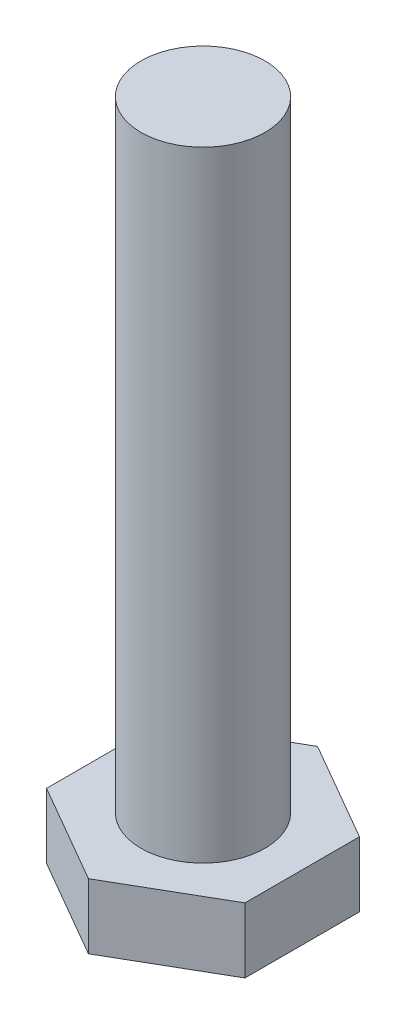
SolidWorks part; units mm, degrees
ref_plane "Спереди" through (0, 0, 0) normal (0, 0, 1) x (1, 0, 0)
ref_plane "Сверху" through (0, 0, 0) normal (0, 1, 0) x (1, 0, 0)
ref_plane "Справа" through (0, 0, 0) normal (1, 0, 0) x (0, 0, -1)
sketch "Эскиз1" plane through (0, 0, 0) normal (0, 1, 0) x (1, 0, 0)
  line L1 (4, -2.3094) -> (4, 2.3094)
  line L2 (4, 2.3094) -> (0, 4.6188)
  line L3 (0, 4.6188) -> (-4, 2.3094)
  line L4 (-4, 2.3094) -> (-4, -2.3094)
  line L5 (-4, -2.3094) -> (0, -4.6188)
  line L6 (0, -4.6188) -> (4, -2.3094)
  circle A0 centre (0, 0) radius 4 construction
extrude "Бобышка-Вытянуть1" add sketch "Эскиз1" along normal blind 3.2
sketch "Эскиз2" plane through (0, 3.2, 0) normal (0, 1, 0) x (1, 0, 0)
  circle A0 centre (0, 0) radius 2.5
extrude "Бобышка-Вытянуть2" add sketch "Эскиз2" along normal blind 25
chamfer "Фаска1" distance 1 angle 30 6 edges at (2, 0, -3.4641) (4, 0, 0) (2, 0, 3.4641) (-2, 0, 3.4641) (-4, 0, 0) (-2, 0, -3.4641)
